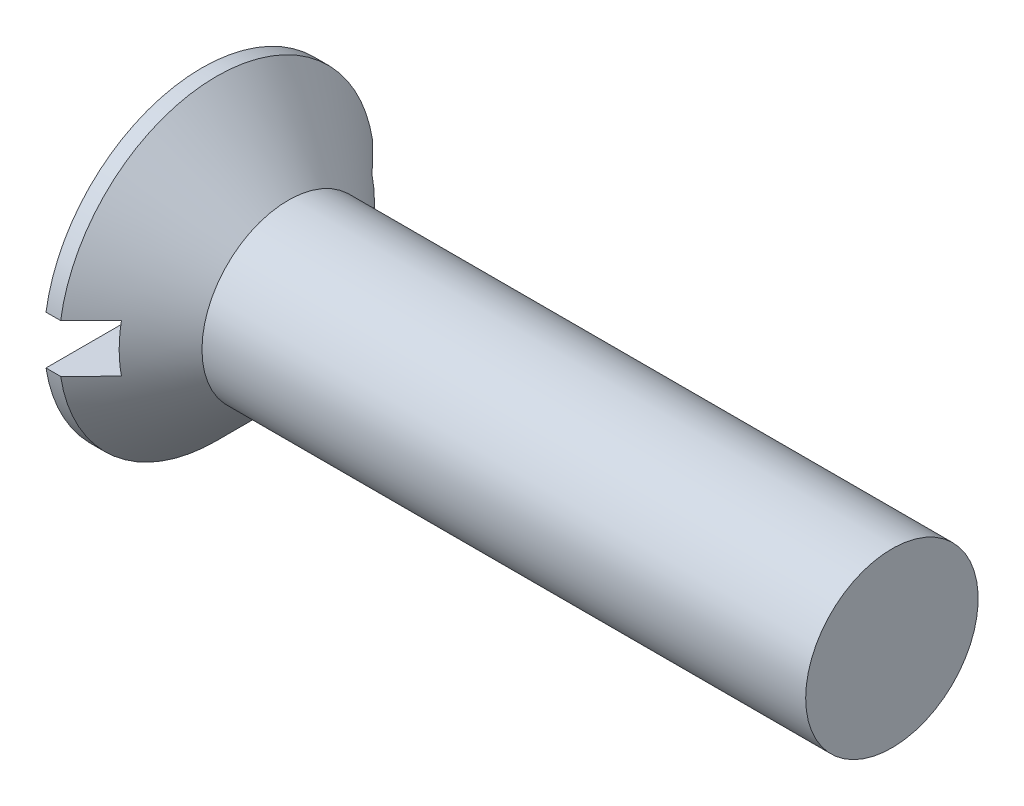
SolidWorks part; units mm, degrees
ref_plane "Plane1" through (0, 0, 0) normal (0, 0, 1) x (1, 0, 0)
ref_plane "Plane2" through (0, 0, 0) normal (0, 1, 0) x (1, 0, 0)
ref_plane "Plane3" through (0, 0, 0) normal (1, 0, 0) x (0, 0, -1)
sketch "BodySke" plane through (0, 0, 0) normal (0, 0, 1) x (1, 0, 0)
  line L0 (0, 0) -> (0, 9.15)
  line L1 (0, 9.15) -> (0.85, 9.15)
  line L2 (5, 5) -> (40, 5)
  line L3 (40, 5) -> (40, 0)
  line L4 (40, 0) -> (0, 0)
  line L5 (-6.35, 0) -> (82.55, 0) construction
  line L6 (5, -5) -> (40, -5) construction
  line L7 (0.85, -9.15) -> (5, -5) construction
  line L8 (0.85, 9.15) -> (5, 5)
  line L9 (0, -9.15) -> (0.85, -9.15) construction
  line L10 (6.5, 6.5875) -> (6.5, -2.9375) construction
  line L11 (5, 6.35) -> (5, -3.175) construction
  dimension "Diameter" = 10
  dimension "Length" = 40
  dimension "Head_ht" = 5
  dimension "Head_dia" = 18.3
  dimension "Head_ang" = 90
  dimension "D6" = 0.85
  dimension "Advance" = 1.5
  dimension "Thread_nom" = 35
revolve "Base-Revolve" add sketch "BodySke" angle 360 about L5
cosmetic thread "ThreadCosmetic" parameters "Thread_length"=33.5, "Thread_minor"=8.344
sketch "Sketch2" plane through (0, 0, 0) normal (-1, 0, 0) x (0, 0, 1)
  line L0 (-9.15, -1.4) -> (9.15, -1.4)
  line L1 (-9.15, -1.4) -> (-9.15, 1.4)
  line L2 (9.15, 1.4) -> (-9.15, 1.4)
  line L3 (9.15, 1.4) -> (9.15, -1.4)
  dimension "D1" = 1.4
  dimension "Slot_width" = 2.8
  dimension "D2" = 18.3
  dimension "D3" = 9.15
extrude "Slot" cut sketch "Sketch2" against normal blind 2.6
sketch "Sketch3" plane through (0, 0, 0) normal (-1, 0, 0) x (0, 0, 1)
  line L0 (-0.99, 4.94) -> (0.99, 4.94)
  line L1 (0.99, 4.94) -> (0.99, -4.94)
  line L2 (0.99, -4.94) -> (-0.99, -4.94)
  line L3 (-0.99, -4.94) -> (-0.99, 4.94)
  dimension "D1" = 4.94
  dimension "Cross_dia" = 9.88
  dimension "D2" = 0.99
  dimension "Cross_width" = 1.98
ref_plane "Plane4" through (5.98, 0, 0) normal (-1, 0, 0) x (0, 0, 1)
sketch "Sketch4" plane through (5.98, 0, 0) normal (-1, 0, 0) x (0, 0, 1)
  line L0 (-0.495, 0.495) -> (0.495, 0.495)
  line L3 (0.495, 0.495) -> (0.495, -0.495)
  line L4 (0.495, -0.495) -> (-0.495, -0.495)
  line L5 (-0.495, -0.495) -> (-0.495, 0.495)
  dimension "D1" = 0.99
  dimension "D2" = 0.99
  dimension "D3" = 0.495
  dimension "D4" = 0.495
loft "Cross" cut profiles "Sketch3", "Sketch4"
pattern_circular "CirPattern1" count 2 every 90 about axis through (0, 0, 0) along (1, 0, 0) of "Cross"
sketch "ThdSchSke" plane through (0, 0, 0) normal (0, 0, 1) x (1, 0, 0)
  line L0 (6.5, -4.172) -> (5.9202, -5)
  line L1 (6.5, -4.172) -> (7.0798, -5)
  line L2 (7.0798, -5) -> (7.0798, -6.25)
  line L3 (-3.175, 0) -> (5.1513, 0) construction
  line L5 (7.0798, -6.25) -> (5.9202, -6.25)
  line L6 (5.9202, -6.25) -> (5.9202, -5)
  line L7 (0, 9.15) -> (0, 1.4) construction
  dimension "Thread_minor" = 8.344
  dimension "Diameter" = 10
  dimension "Start" = 6.5
  dimension "SideAngle" = 55
  dimension "VeeAngle" = 70
  dimension "Overcut" = 12.5
revolve "ThreadSchematic" [suppressed] cut sketch "ThdSchSke" angle 360 about L3
pattern_linear "ThdSchPat" [suppressed]
equation "\"D1@Sketch3\" = \"Cross_dia@Sketch3\" / 2"
equation "\"D2@Sketch3\" = \"Cross_width@Sketch3\" / 2"
equation "\"D1@Sketch4\" = \"Cross_width@Sketch3\" *.5"
equation "\"D2@Sketch4\" = \"D1@Sketch4\""
equation "\"D4@Sketch4\" = \"D2@Sketch4\" / 2"
equation "\"D3@Sketch4\" = \"D1@Sketch4\" / 2"
equation "\"D1@Sketch2\" = \"Slot_width@Sketch2\" / 2"
equation "\"D2@Sketch2\" = \"Head_dia@BodySke\""
equation "\"D3@Sketch2\" = \"D2@Sketch2\" / 2"
equation "\"Thread_length@ThreadCosmetic\" = ((sgn( (\"Length@BodySke\" - \"Advance@BodySke\" - \"Head_ht@BodySke\" ) - \"Thread_nom@BodySke\" )-1)*( (\"Length@BodySke\" - \"Advance@BodySke\" - \"Head_ht@BodySke\" ) - \"Thread_nom@BodySke\" ))/-2+ \"Thread_nom@BodySke\""
equation "\"Thread_minor@ThdSchSke\" = \"Thread_minor@ThreadCosmetic\""
equation "\"Diameter@ThdSchSke\" = \"Diameter@BodySke\""
equation "\"Overcut@ThdSchSke\" = \"Diameter@BodySke\" * 1.25"
equation "\"Start@ThdSchSke\" = 0.000001 + \"Length@BodySke\" - \"Thread_length@ThreadCosmetic\"  '---Countersunk---"
equation "\"Num_threads@ThdSchPat\" = int( \"Thread_length@ThreadCosmetic\" / \"Advance@BodySke\" + 0.999 )  + 1"
equation "\"Advance@ThdSchPat\" = \"Thread_length@ThreadCosmetic\" /  (\"Num_threads@ThdSchPat\" - 1) 'relax it"
